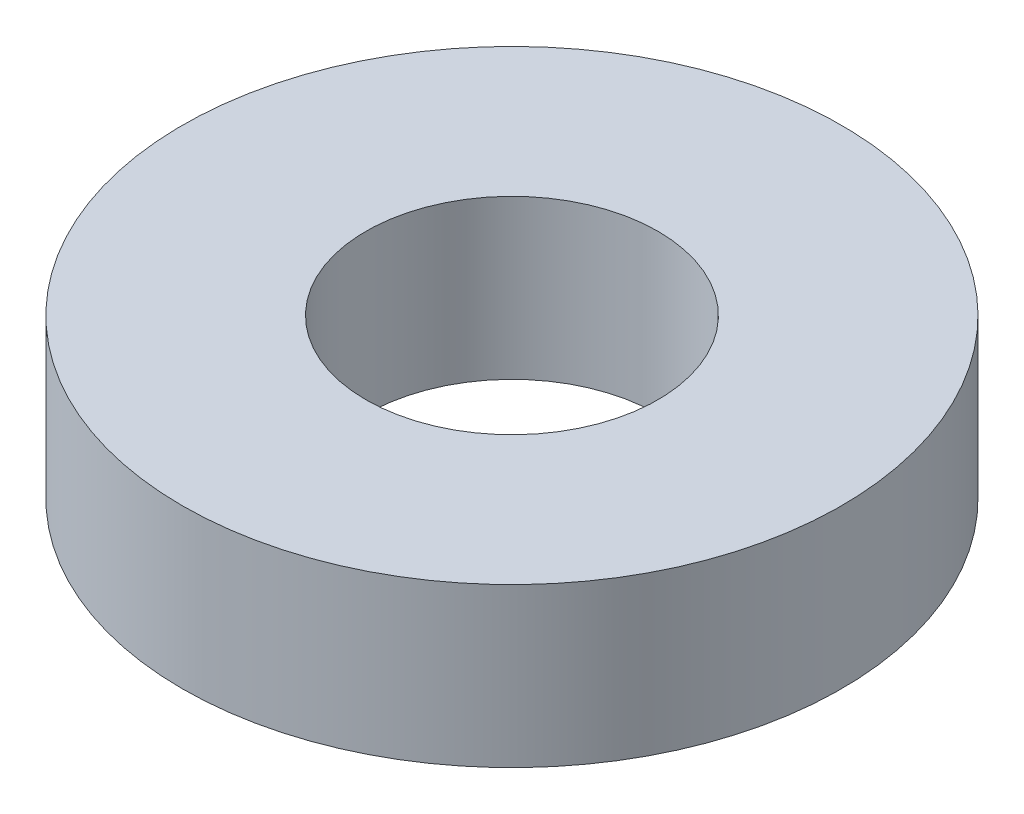
SolidWorks part; units mm, degrees
ref_plane "Front Plane" through (0, 0, 0) normal (0, 0, 1) x (1, 0, 0)
ref_plane "Top Plane" through (0, 0, 0) normal (0, 1, 0) x (1, 0, 0)
ref_plane "Right Plane" through (0, 0, 0) normal (1, 0, 0) x (0, 0, -1)
sketch "Sketch1" plane through (0, 0, 0) normal (0, 1, 0) x (1, 0, 0)
  circle A0 centre (0, 0) radius 3.95
  circle A1 centre (0, 0) radius 1.75
  dimension "D1" = 7.9
  dimension "D2" = 3.5
extrude "Boss-Extrude1" add sketch "Sketch1" along normal blind 1.9
